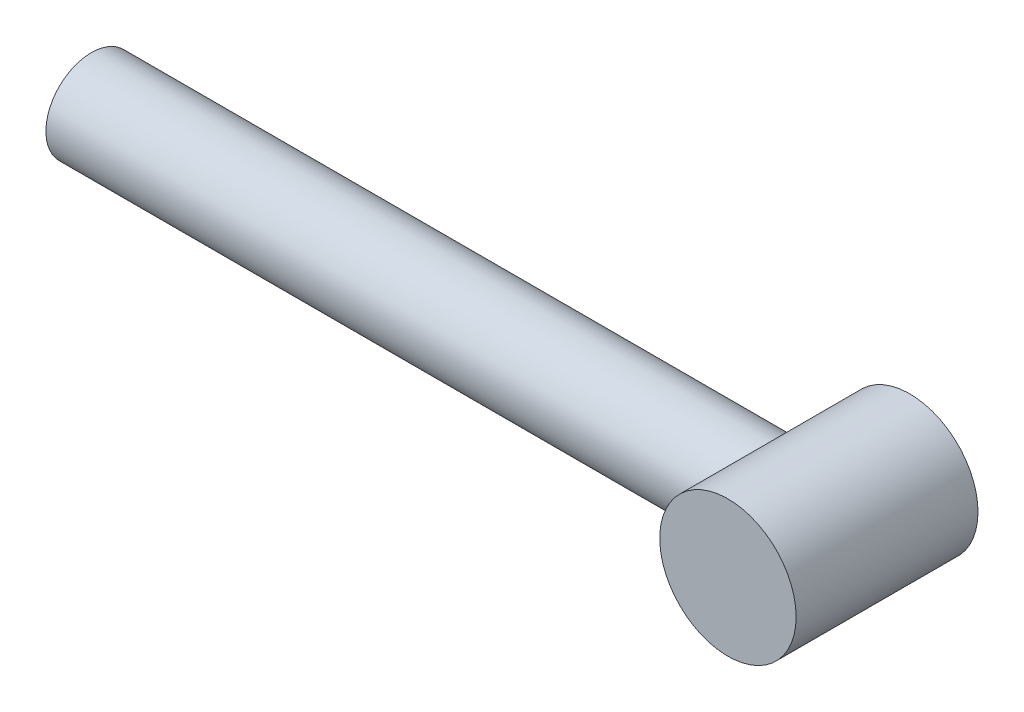
SolidWorks part; units mm, degrees
ref_plane "Front" through (0, 0, 0) normal (0, 0, 1) x (1, 0, 0)
ref_plane "Top" through (0, 0, 0) normal (0, 1, 0) x (1, 0, 0)
ref_plane "Right" through (0, 0, 0) normal (1, 0, 0) x (0, 0, -1)
sketch "Sketch1" plane through (0, 0, 0) normal (0, 0, 1) x (1, 0, 0)
  circle A0 centre (0, 0) radius 2.3813
  dimension "D1" = 4.7625
extrude "Brake Cable Anchor Cylinder" add sketch "Sketch1" along normal mid plane 6.35
sketch "Sketch3" plane through (0, 0, 0) normal (1, 0, 0) x (0, 0, -1)
  circle A0 centre (0, 0) radius 1.5875
  dimension "D1" = 3.175
extrude "Brake Cable (simulated)" add sketch "Sketch3" against normal blind 25.4
